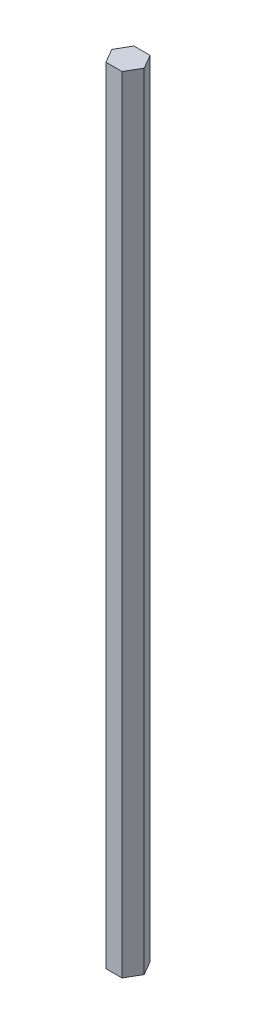
SolidWorks part; units mm, degrees
ref_plane "Front Plane" through (0, 0, 0) normal (0, 0, 1) x (1, 0, 0)
ref_plane "Top Plane" through (0, 0, 0) normal (0, 1, 0) x (1, 0, 0)
ref_plane "Right Plane" through (0, 0, 0) normal (1, 0, 0) x (0, 0, -1)
sketch "Sketch1" plane through (0, 0, 0) normal (0, 1, 0) x (1, 0, 0)
  line L1 (3.6662, 6.35) -> (-3.6662, 6.35)
  line L2 (-3.6662, 6.35) -> (-7.3323, 0)
  line L3 (-7.3323, 0) -> (-3.6662, -6.35)
  line L4 (-3.6662, -6.35) -> (3.6662, -6.35)
  line L5 (3.6662, -6.35) -> (7.3323, 0)
  line L6 (7.3323, 0) -> (3.6662, 6.35)
  circle A0 centre (0, 0) radius 6.35 construction
  point P1 (0, 6.35)
  dimension "D1" = 12.7
extrude "Boss-Extrude1" add sketch "Sketch1" along normal blind 355.6
